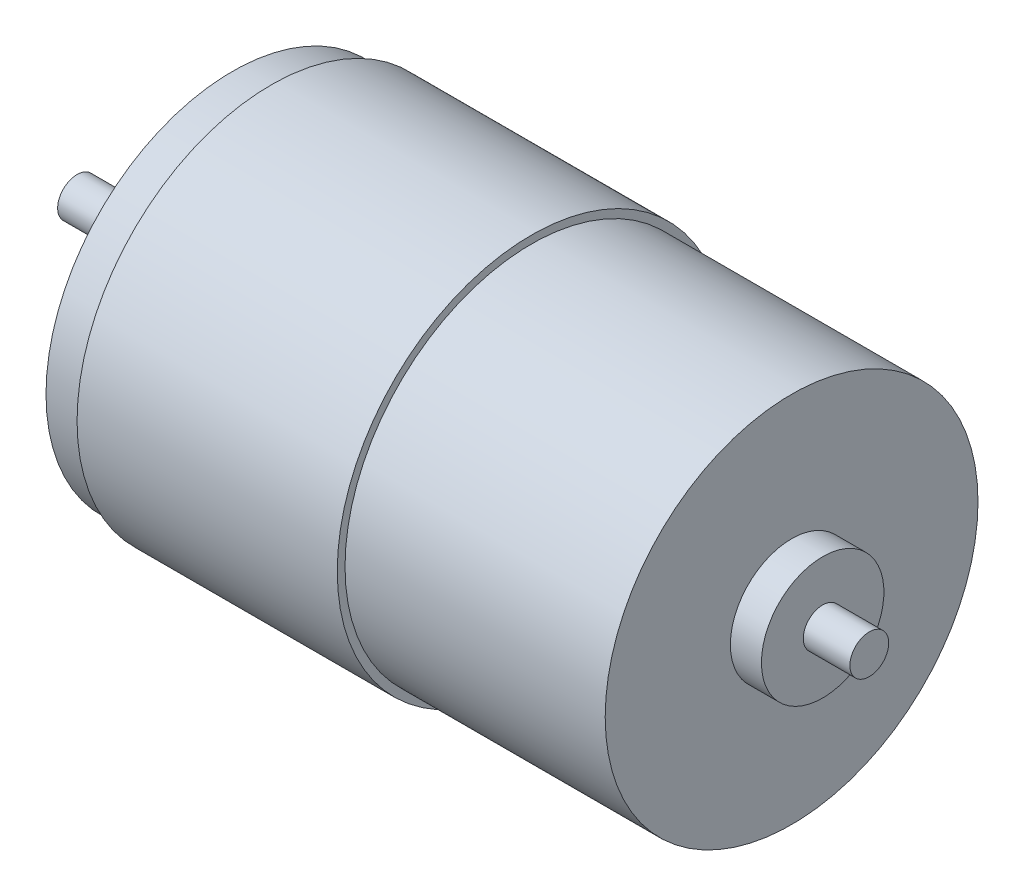
SolidWorks part; units mm, degrees
ref_plane "前视基准面" through (0, 0, 0) normal (0, 0, 1) x (1, 0, 0)
ref_plane "上视基准面" through (0, 0, 0) normal (0, 1, 0) x (1, 0, 0)
ref_plane "右视基准面" through (0, 0, 0) normal (1, 0, 0) x (0, 0, -1)
sketch "草图1" plane through (0, 0, 0) normal (0, 1, 0) x (1, 0, 0)
  line L0 (-8.1235, 0) -> (99.6879, 0) construction
  line L1 (-6.7439, 0) -> (-6.7439, 2.5)
  line L2 (-6.7439, 2.5) -> (9.2561, 2.5)
  line L3 (9.2561, 2.5) -> (9.2561, 0)
  line L4 (9.2561, 0) -> (9.2561, 9)
  line L5 (9.2561, 9) -> (13.2561, 9)
  line L6 (13.2561, 9) -> (13.2561, 0)
  line L7 (13.2561, 0) -> (13.2561, 24)
  line L8 (13.2561, 24) -> (18.2561, 24)
  line L9 (18.2561, 24) -> (18.2561, 0)
  line L10 (18.2561, 0) -> (18.2561, 25)
  line L11 (18.2561, 25) -> (51.7561, 25)
  line L12 (51.7561, 25) -> (51.7561, 0)
  line L13 (51.7561, 0) -> (51.7561, 24)
  line L14 (51.7561, 24) -> (85.2561, 24)
  line L15 (85.2561, 24) -> (85.2561, -0.1154)
  line L16 (85.2561, -0.1154) -> (85.2561, 7.8846)
  line L17 (85.2561, 7.8846) -> (89.2561, 7.8846)
  line L18 (89.2561, 7.8846) -> (89.2561, 0)
  line L19 (89.2561, 0) -> (89.2561, 2.5)
  line L20 (89.2561, 2.5) -> (95.2561, 2.5)
  line L21 (95.2561, 2.5) -> (95.2561, 0)
  dimension "D1" = 2.5
  dimension "D2" = 16
  dimension "D3" = 9
  dimension "D4" = 4
  dimension "D5" = 24
  dimension "D6" = 5
  dimension "D7" = 25
  dimension "D8" = 33.5
  dimension "D9" = 24
  dimension "D10" = 33.5
  dimension "D11" = 8
  dimension "D12" = 4
  dimension "D13" = 2.5
  dimension "D14" = 6
revolve "旋转1" add sketch "草图1" angle 360 about L0
sketch "草图2" plane through (13.2561, 0, 0) normal (-1, 0, 0) x (0, 0, 1)
  line L0 (-24, 0) -> (24, 0) construction
  line L1 (0, 24) -> (0, -24) construction
  circle A0 centre (0, 0) radius 24 construction
  circle A1 centre (0, 0) radius 24 construction
  circle A2 centre (0, 14.5) radius 2
  circle A3 centre (0, -14.5) radius 2
  circle A4 centre (-16, 0) radius 2.5
  circle A5 centre (16, 0) radius 2.5
  dimension "D1" = 29
  dimension "D2" = 32
  dimension "D3" = 4
  dimension "D4" = 5
extrude "切除-拉伸1" cut sketch "草图2" against normal blind 2
